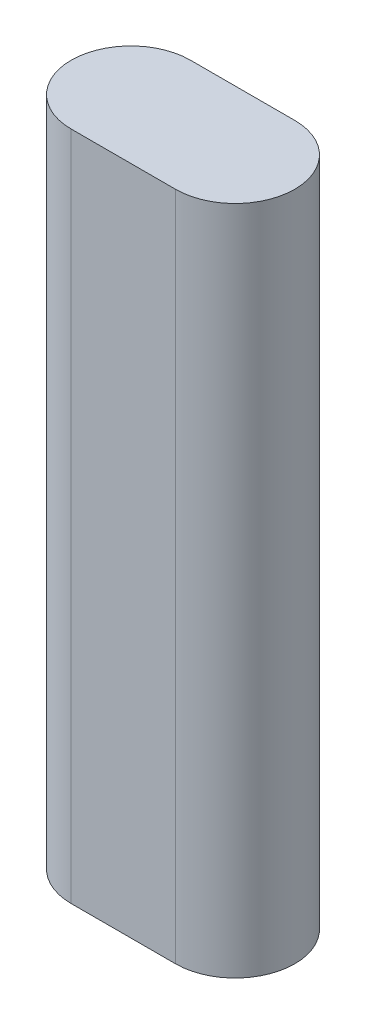
SolidWorks part; units mm, degrees
ref_plane "Front Plane" through (0, 0, 0) normal (0, 0, 1) x (1, 0, 0)
ref_plane "Top Plane" through (0, 0, 0) normal (0, 1, 0) x (1, 0, 0)
ref_plane "Right Plane" through (0, 0, 0) normal (1, 0, 0) x (0, 0, -1)
sketch "Sketch1" plane through (0, 0, 0) normal (0, 1, 0) x (1, 0, 0)
  line L0 (-10.5, 0) -> (10.5, 0) construction
  line L1 (-10.5, 12) -> (10.5, 12)
  line L2 (-10.5, -12) -> (10.5, -12)
  arc A0 (-10.5, 12) -> (-10.5, -12) centre (-10.5, 0) ccw
  arc A1 (10.5, -12) -> (10.5, 12) centre (10.5, 0) ccw
  point P2 (0, 0)
  point P8 (-22.5, 0)
  point P9 (22.5, 0)
  dimension "D1" = 24
  dimension "D2" = 45
extrude "Boss-Extrude1" add sketch "Sketch1" along normal blind 135
